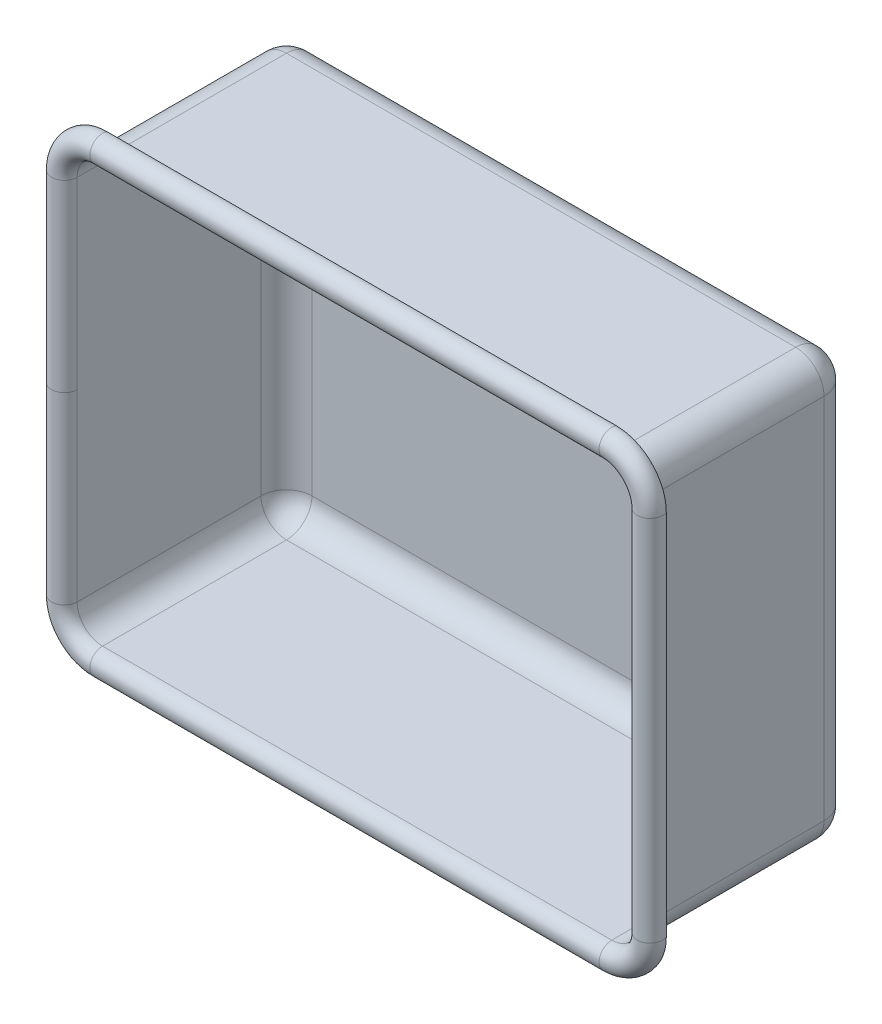
SolidWorks part; units mm, degrees
material "ABS"
ref_plane "Front Plane" through (0, 0, 0) normal (0, 0, 1) x (1, 0, 0)
ref_plane "Top Plane" through (0, 0, 0) normal (0, 1, 0) x (1, 0, 0)
ref_plane "Right Plane" through (0, 0, 0) normal (1, 0, 0) x (0, 0, -1)
sketch "Sketch1" plane through (0, 0, 0) normal (0, 0, 1) x (1, 0, 0)
  line L1 (200, 150) -> (-200, 150)
  line L2 (200, 150) -> (200, -150)
  line L3 (200, -150) -> (-200, -150)
  line L4 (-200, 150) -> (-200, -150)
  line L5 (200, 150) -> (-200, -150) construction
  line L6 (200, -150) -> (-200, 150) construction
  line L11 (198, -148.5) -> (-198, 148.5) construction
  line L12 (198, 148.5) -> (-198, -148.5) construction
  point P0 (0, 0)
  point P10 (-198, -148.5)
  dimension "D1" = 300
  dimension "D2" = 400
extrude "Boss-Extrude1" add sketch "Sketch1" along normal blind 150
fillet "Fillet1" radius 20 8 edges at (0, -150, 0) (200, 0, 0) (0, 150, 0) (-200, 0, 0) (-200, -150, 75) (200, -150, 75) (200, 150, 75) (-200, 150, 75)
shell "Shell1" thickness 2
sketch "Sketch2" plane through (0, 0, 0) normal (0, 1, 0) x (1, 0, 0)
  line L0 (-198, -150) -> (-200, -150)
  line L1 (-207, -150) -> (-215.4572, -146.9218) construction
  line L2 (-215.4572, -146.9218) -> (-213.5778, -147.6059)
  arc A0 (-213.5778, -147.6059) -> (-200, -150) centre (-207, -150) ccw
  arc A1 (-215.4572, -146.9218) -> (-198, -150) centre (-207, -150) ccw
  dimension "D2" = 14
  dimension "D3" = 2
  dimension "D4" = 150
  dimension "D1" = 207
  dimension "D5" = 200
sketch "Sketch3" plane through (0, 0, 150) normal (0, 0, 1) x (1, 0, 0)
  line L0 (-180, -148) -> (180, -148) construction
  line L1 (198, -130) -> (198, 130) construction
  line L2 (180, 148) -> (-180, 148) construction
  line L3 (-198, 130) -> (-198, -130) construction
  line L4 (-180, -148) -> (180, -148)
  line L5 (198, -130) -> (198, 130)
  line L6 (180, 148) -> (-180, 148)
  line L7 (-198, 130) -> (-198, -130)
  arc A0 (-198, -130) -> (-180, -148) centre (-180, -130) ccw construction
  arc A1 (180, -148) -> (198, -130) centre (180, -130) ccw construction
  arc A2 (198, 130) -> (180, 148) centre (180, 130) ccw construction
  arc A3 (-180, 148) -> (-198, 130) centre (-180, 130) ccw construction
  arc A4 (-198, -130) -> (-180, -148) centre (-180, -130) ccw
  arc A5 (180, -148) -> (198, -130) centre (180, -130) ccw
  arc A6 (198, 130) -> (180, 148) centre (180, 130) ccw
  arc A7 (-180, 148) -> (-198, 130) centre (-180, 130) ccw
sweep "Sweep2" add profiles "Sketch2" path "Sketch3"
